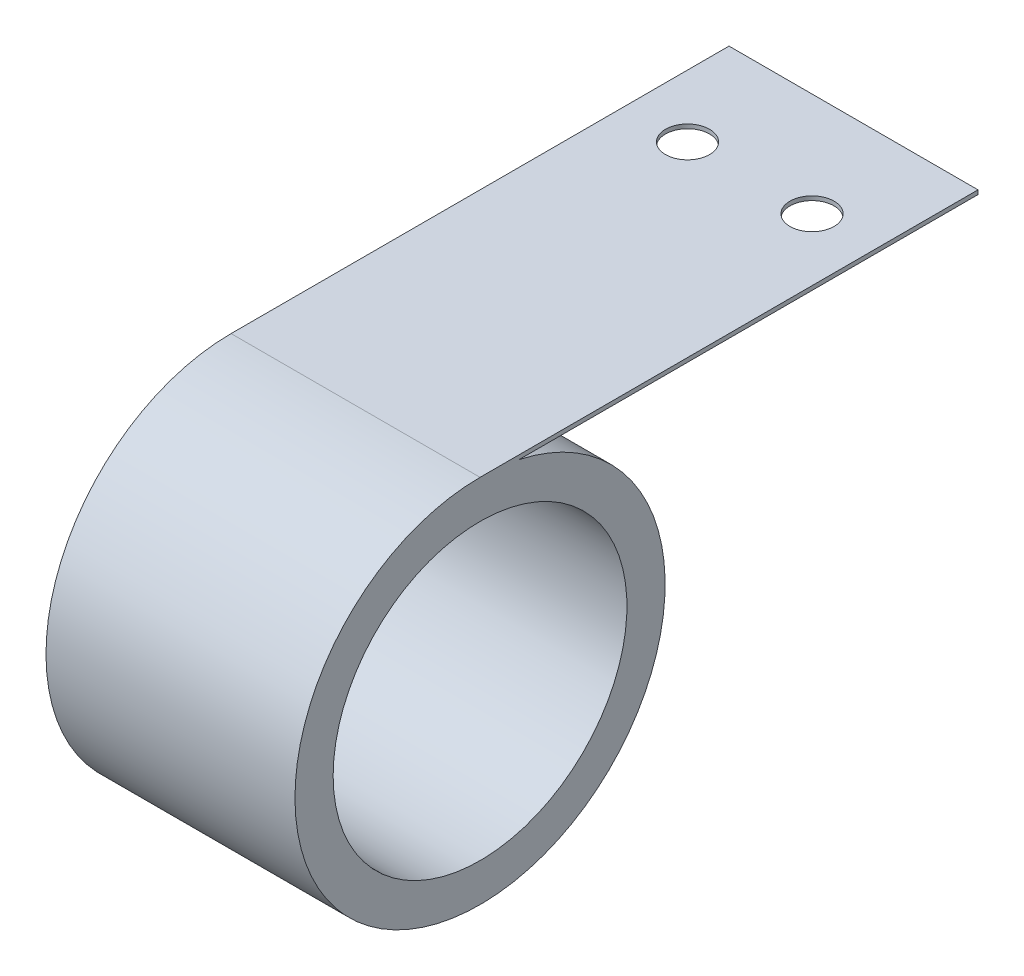
SolidWorks part; units mm, degrees
ref_plane "Front" through (0, 0, 0) normal (0, 0, 1) x (1, 0, 0)
ref_plane "Top" through (0, 0, 0) normal (0, 1, 0) x (1, 0, 0)
ref_plane "Right" through (0, 0, 0) normal (1, 0, 0) x (0, 0, -1)
sketch "Sketch1" plane through (0, 0, 0) normal (1, 0, 0) x (0, 0, -1)
  line L0 (0, 28.321) -> (76.2, 28.321)
  line L1 (5.9636, 27.686) -> (76.2, 27.686)
  line L2 (76.2, 27.686) -> (76.2, 28.321)
  line L3 (0, 28.321) -> (0, -28.321) construction
  circle A0 centre (0, 0) radius 22.479
  arc A1 (0, 28.321) -> (5.9636, 27.686) centre (0, 0) ccw
  dimension "D2" = 76.2
extrude "Boss-Extrude1" add sketch "Sketch1" along normal mid plane 38.1
sketch "Sketch2" plane through (0, 28.321, 0) normal (0, 1, 0) x (1, 0, 0)
  line L0 (0, -304.8) -> (0, 76.2) construction
  line L1 (19.05, 76.2) -> (-19.05, 76.2) construction
  line L2 (-19.05, 75.7235) -> (-19.05, 76.835)
  line L3 (-19.05, 76.2) -> (-19.05, 0) construction
  line L4 (-19.05, 76.835) -> (19.05, 76.835)
  line L5 (19.05, 75.7235) -> (19.05, 76.835)
  line L6 (19.05, 76.2) -> (19.05, 0) construction
  arc A0 (19.05, 75.7235) -> (-19.05, 75.7235) centre (0, -304.8) ccw
  circle A1 centre (0, 60.325) radius 3.3655
  dimension "D2" = 0.635
extrude "OneHole" [suppressed] cut sketch "Sketch2" against normal up to next
sketch "Sketch4" plane through (0, 28.321, 0) normal (0, 1, 0) x (1, 0, 0)
  line L0 (0, 76.2) -> (0, 60.325) construction
  line L1 (-9.525, 60.325) -> (-9.525, 76.2) construction
  line L2 (9.525, 60.325) -> (-9.525, 60.325) construction
  line L3 (19.05, 76.2) -> (-19.05, 76.2) construction
  circle A0 centre (-9.525, 60.325) radius 3.3655
  circle A1 centre (9.525, 60.325) radius 3.3655
  dimension "D1" = 6.731
  dimension "D2" = 15.875
  dimension "D3" = 19.05
extrude "TwoHole" cut sketch "Sketch4" against normal up to next
equation "\"D2@Sketch1\" = \"Width@Boss-Extrude1\"*2"
equation "\"D1@Sketch4\" = \"HoleDia@Sketch2\""
equation "\"D2@Sketch4\" = \"HolePosition@Sketch2\""
